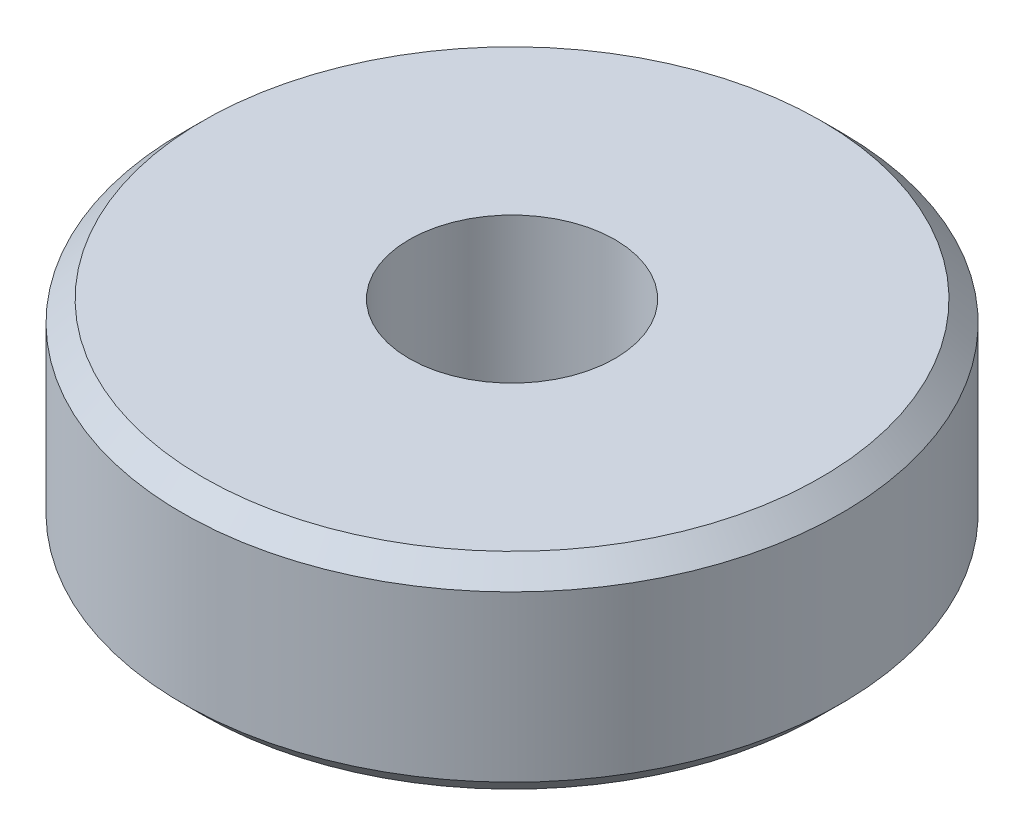
SolidWorks part; units mm, degrees
ref_plane "Front Plane" through (0, 0, 0) normal (0, 0, 1) x (1, 0, 0)
ref_plane "Top Plane" through (0, 0, 0) normal (0, 1, 0) x (1, 0, 0)
ref_plane "Right Plane" through (0, 0, 0) normal (1, 0, 0) x (0, 0, -1)
sketch "Sketch1" plane through (0, 0, 0) normal (0, 0, 1) x (1, 0, 0)
  line L0 (0, 0) -> (2.5, 0) construction
  line L1 (7.5, 5) -> (8, 4.5)
  line L2 (2.5, 0) -> (7.5, 0)
  line L3 (2.5, 0) -> (2.5, 5)
  line L4 (2.5, 5) -> (7.5, 5)
  line L5 (8, 0.5) -> (8, 4.5)
  line L6 (7.5, 0) -> (8, 0.5)
  line L7 (0, 0) -> (0, 3.8029) construction
  point P3 (8, 5)
  point P5 (8, 0)
  dimension "D1" = 5
  dimension "D2" = 8
  dimension "D5" = 2.5
revolve "Revolve1" add sketch "Sketch1" angle 360 about L7
